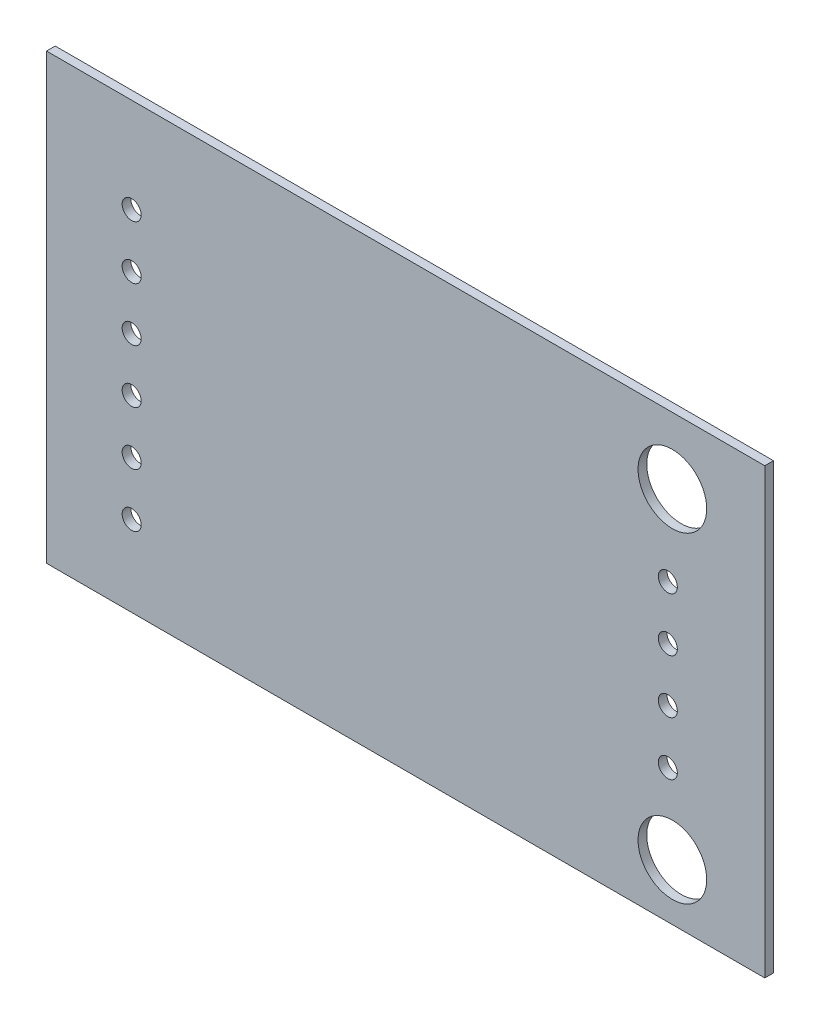
SolidWorks part; units mm, degrees
ref_plane "Plano frontal" through (0, 0, 0) normal (0, 0, 1) x (1, 0, 0)
ref_plane "Plano superior" through (0, 0, 0) normal (0, 1, 0) x (1, 0, 0)
ref_plane "Plano direito" through (0, 0, 0) normal (1, 0, 0) x (0, 0, -1)
ref_plane "Plano1" through (0, 0, 0.4115) normal (0, 0, 1) x (1, 0, 0)
sketch "Esboço1" plane through (0, 0, 0.4115) normal (0, 0, 1) x (1, 0, 0)
  line L0 (0, 0) -> (34, 0)
  line L1 (34, 0) -> (34, 21)
  line L2 (34, 21) -> (0, 21)
  line L3 (0, 21) -> (0, 0)
  circle A0 centre (29.4099, 11.4118) radius 0.45
  circle A1 centre (29.4099, 8.8718) radius 0.45
  circle A2 centre (29.4099, 13.9518) radius 0.45
  circle A3 centre (29.4099, 6.3318) radius 0.45
  circle A4 centre (4.0307, 3.8155) radius 0.45
  circle A5 centre (4.0307, 13.9755) radius 0.45
  circle A6 centre (4.0307, 11.4355) radius 0.45
  circle A7 centre (4.0307, 16.5155) radius 0.45
  circle A8 centre (4.0307, 6.3555) radius 0.45
  circle A9 centre (4.0307, 8.8955) radius 0.45
extrude "Ressalto-extrusão1" add sketch "Esboço1" against normal blind 0.4115
sketch "Esboço2" plane through (0, 0, 0.4115) normal (0, 0, 1) x (1, 0, 0)
  circle A0 centre (29.625, 17.858) radius 1.625
  circle A1 centre (29.625, 2.6582) radius 1.625
  dimension "D1" = 3.25
extrude "Corte-extrusão1" cut sketch "Esboço2" against normal through all
